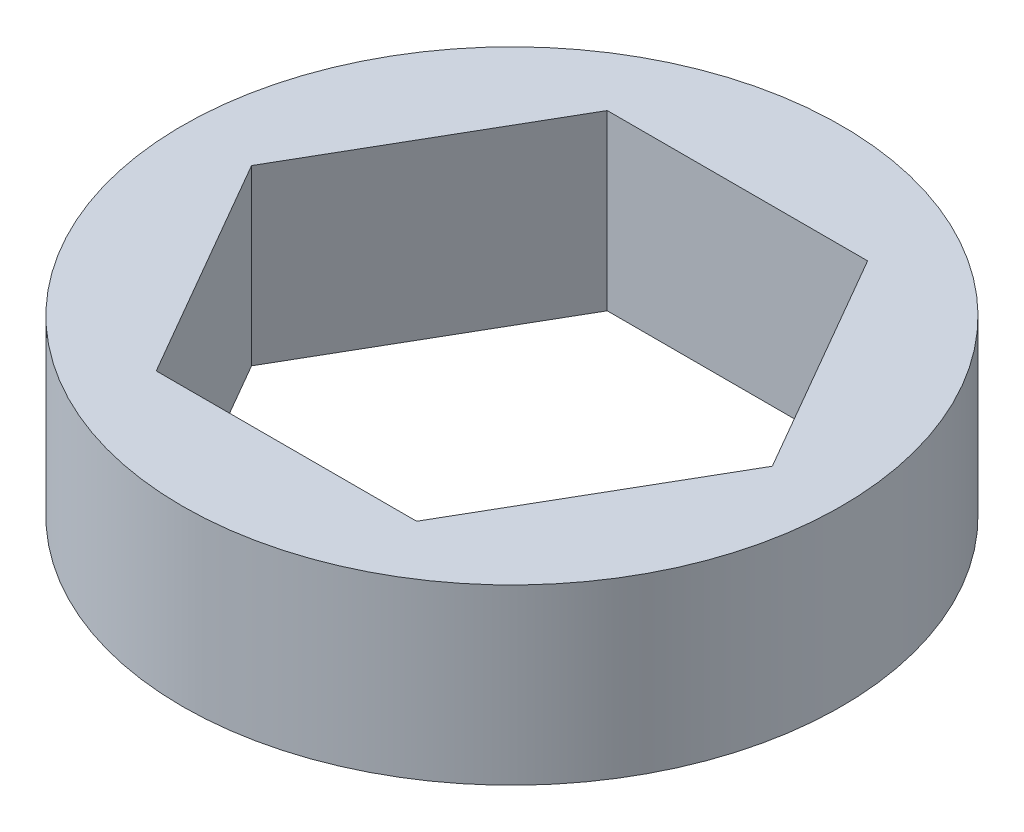
SolidWorks part; units mm, degrees
ref_plane "Front Plane" through (0, 0, 0) normal (0, 0, 1) x (1, 0, 0)
ref_plane "Top Plane" through (0, 0, 0) normal (0, 1, 0) x (1, 0, 0)
ref_plane "Right Plane" through (0, 0, 0) normal (1, 0, 0) x (0, 0, -1)
sketch "Sketch1" plane through (0, 0, 0) normal (0, 1, 0) x (1, 0, 0)
  line L0 (0, 0) -> (35.7746, 0) construction
  line L1 (7.5056, 0) -> (3.7528, 6.5)
  line L2 (3.7528, 6.5) -> (-3.7528, 6.5)
  line L3 (-3.7528, 6.5) -> (-7.5056, 0)
  line L4 (-7.5056, 0) -> (-3.7528, -6.5)
  line L5 (-3.7528, -6.5) -> (3.7528, -6.5)
  line L6 (3.7528, -6.5) -> (7.5056, 0)
  circle A0 centre (0, 0) radius 6.5 construction
  circle A1 centre (0, 0) radius 9.5
  dimension "D1" = 13
  dimension "D2" = 19
extrude "Boss-Extrude1" add sketch "Sketch1" along normal blind 5
